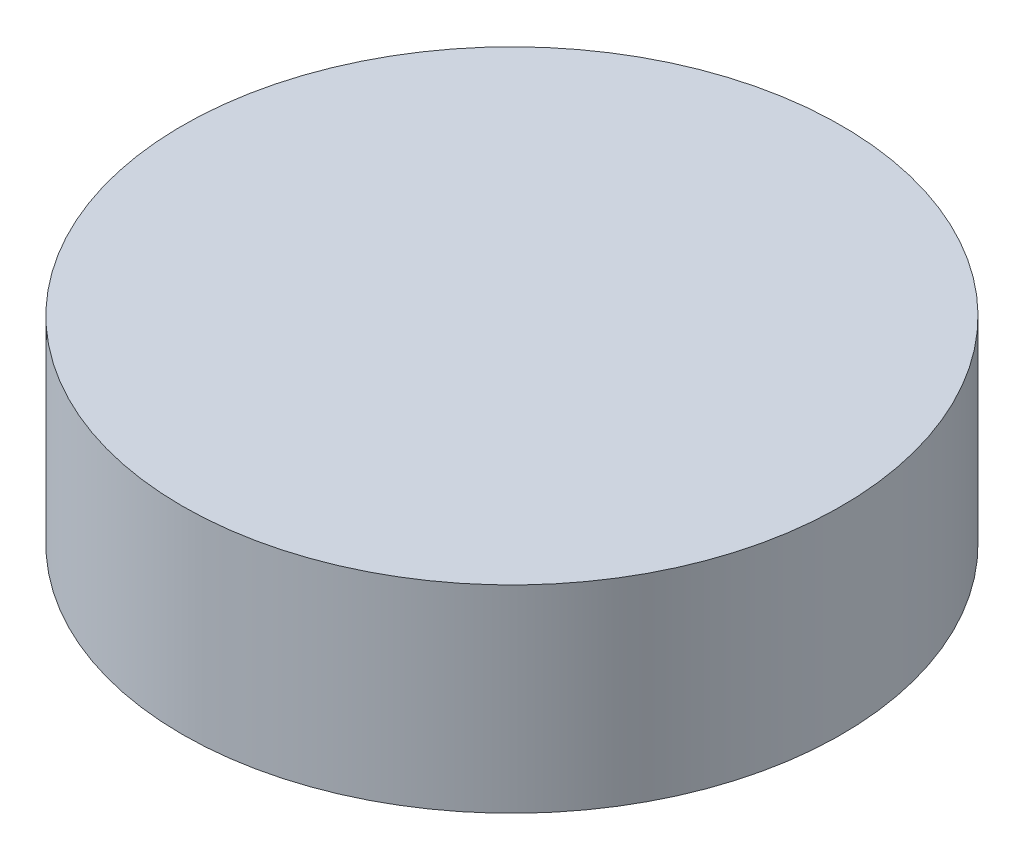
SolidWorks part; units mm, degrees
material "5052-O"
ref_plane "正面" through (0, 0, 0) normal (0, 0, 1) x (1, 0, 0)
ref_plane "平面" through (0, 0, 0) normal (0, 1, 0) x (1, 0, 0)
ref_plane "右側面" through (0, 0, 0) normal (1, 0, 0) x (0, 0, -1)
sketch "ｽｹｯﾁ1" plane through (0, 0, 0) normal (0, 1, 0) x (1, 0, 0)
  circle A0 centre (0, 0) radius 2.5
extrude "ﾎﾞｽ - 押し出し1" add sketch "ｽｹｯﾁ1" along normal blind 2
sketch "ｽｹｯﾁ2" plane through (0, 2, 0) normal (0, 1, 0) x (1, 0, 0)
  circle A0 centre (0, 0) radius 2.5
extrude "ﾎﾞｽ - 押し出し2" add sketch "ｽｹｯﾁ2" along normal blind 0.5
sketch "ｽｹｯﾁ3" plane through (0, 2.5, 0) normal (0, 1, 0) x (1, 0, 0)
  circle A0 centre (0, 0) radius 2.5
extrude "ｶｯﾄ - 押し出し1" cut sketch "ｽｹｯﾁ3" against normal blind 1
